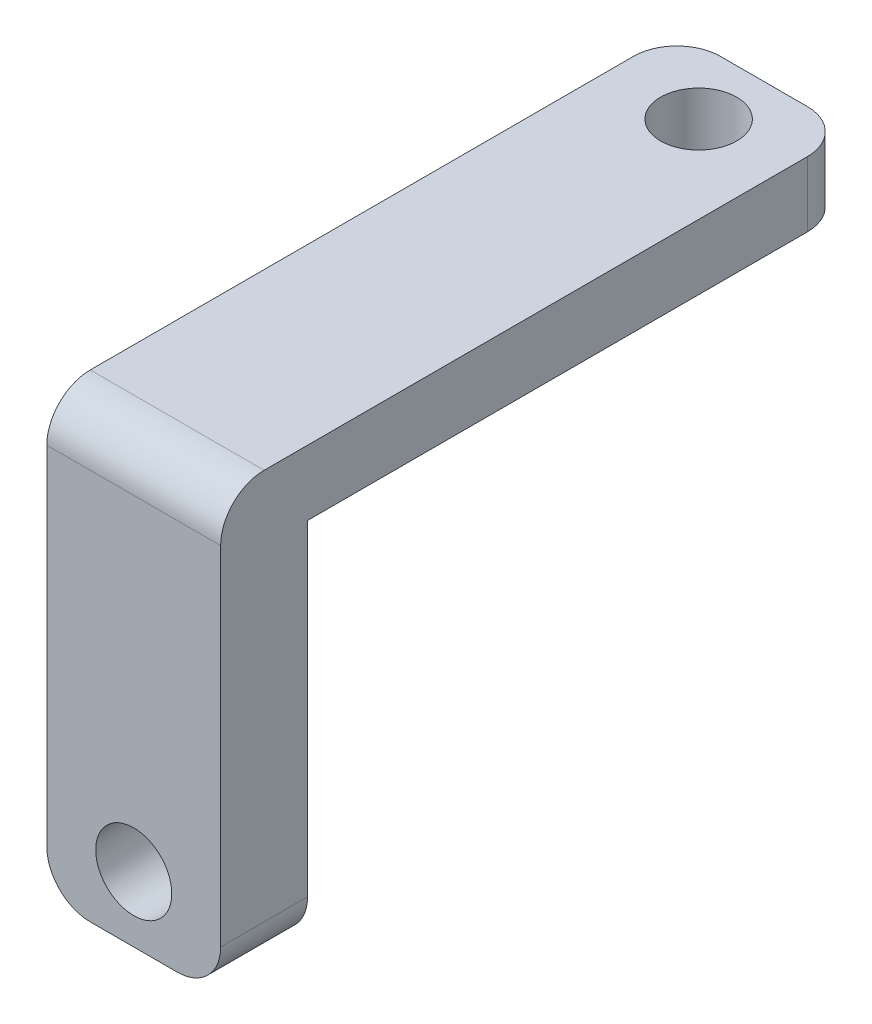
SolidWorks part; units mm, degrees
ref_plane "Plan de face" through (0, 0, 0) normal (0, 0, 1) x (1, 0, 0)
ref_plane "Plan de dessus" through (0, 0, 0) normal (0, 1, 0) x (1, 0, 0)
ref_plane "Plan de droite" through (0, 0, 0) normal (1, 0, 0) x (0, 0, -1)
sketch "Esquisse1" plane through (0, 0, 0) normal (0, 1, 0) x (1, 0, 0)
  line L1 (-4, 12.5) -> (4, 12.5)
  line L2 (-4, 12.5) -> (-4, -12.5)
  line L3 (-4, -12.5) -> (4, -12.5)
  line L4 (4, 12.5) -> (4, -12.5)
  circle A0 centre (0, 9.5) radius 1.75
  point P4 (0, 12.5)
  point P5 (-4, 0)
  dimension "D2" = 3
  dimension "D3" = 3.5
  dimension "D1" = 25
  dimension "D4" = 8
extrude "Boss.-Extru.1" add sketch "Esquisse1" along normal blind 3
sketch "Esquisse2" plane through (0, 0, 12.5) normal (0, 0, 1) x (1, 0, 0)
  line L0 (4, 3) -> (4, 0) construction
  line L1 (-4, 3) -> (4, 3)
  line L2 (-4, 3) -> (-4, -17)
  line L3 (-4, -17) -> (4, -17)
  line L4 (4, 3) -> (4, -17)
  line L5 (-4, 3) -> (4, 3) construction
  circle A0 centre (0, -14) radius 1.75
  dimension "D1" = 3.5
  dimension "D2" = 17
  dimension "D3" = 20
extrude "Boss.-Extru.2" add sketch "Esquisse2" along normal blind 4
fillet "Congé1" radius 2 5 edges at (4, -17, 14.5) (-4, -17, 14.5) (-4, 1.5, -12.5) (4, 1.5, -12.5) (0, 3, 16.5)
